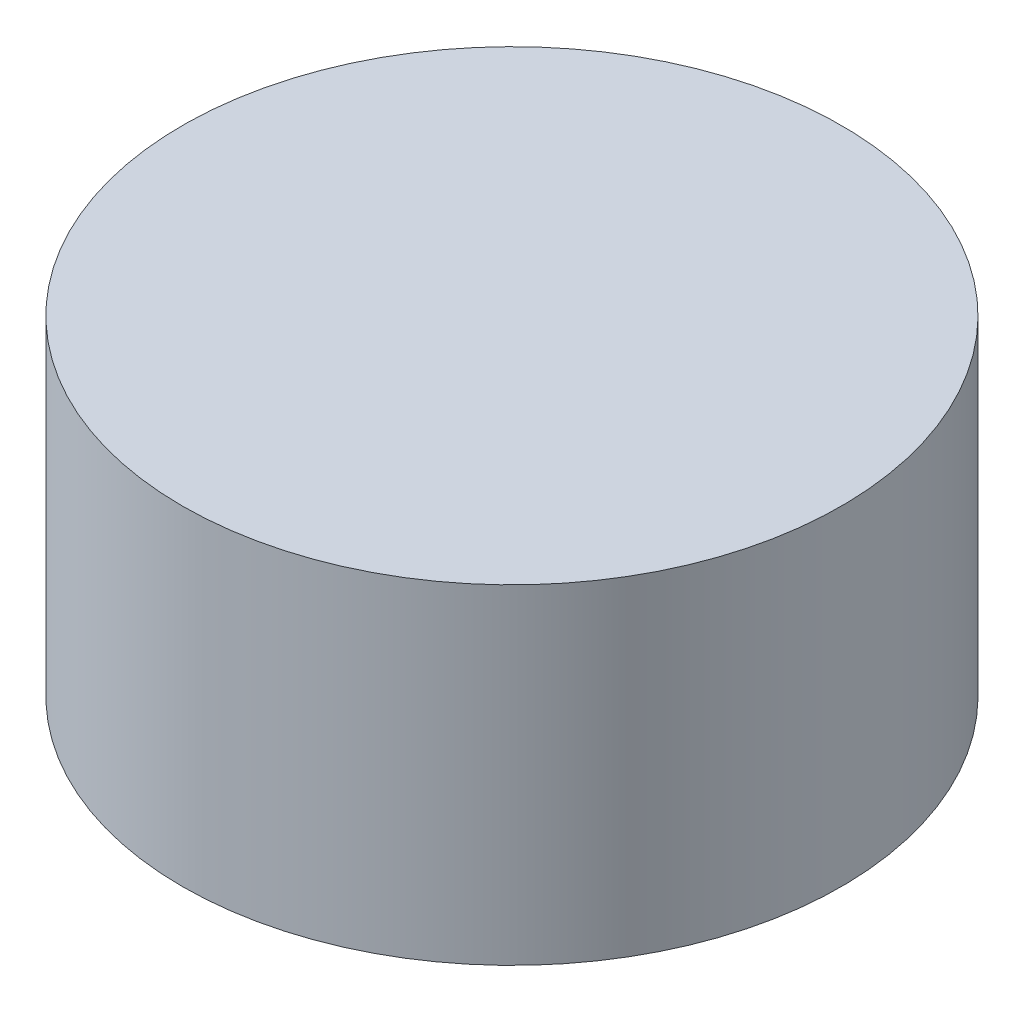
SolidWorks part; units mm, degrees
ref_plane "Front Plane" through (0, 0, 0) normal (0, 0, 1) x (1, 0, 0)
ref_plane "Top Plane" through (0, 0, 0) normal (0, 1, 0) x (1, 0, 0)
ref_plane "Right Plane" through (0, 0, 0) normal (1, 0, 0) x (0, 0, -1)
sketch "Sketch1" plane through (0, 0, 0) normal (0, 1, 0) x (1, 0, 0)
  circle A0 centre (0, 0) radius 90
  dimension "D1" = 180
extrude "Boss-Extrude1" add sketch "Sketch1" along normal blind 90
